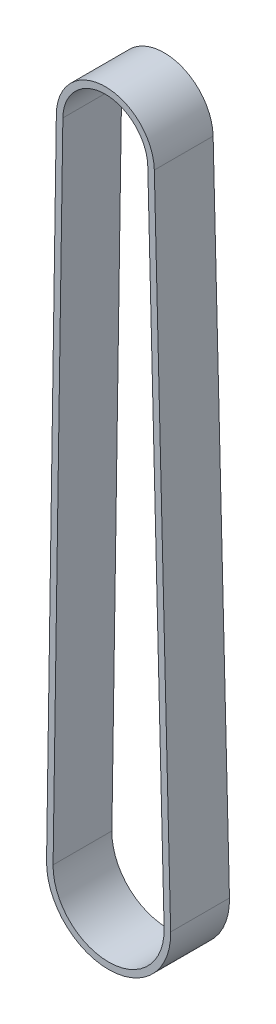
SolidWorks part; units mm, degrees
ref_plane "Front Plane" through (0, 0, 0) normal (0, 0, 1) x (1, 0, 0)
ref_plane "Top Plane" through (0, 0, 0) normal (0, 1, 0) x (1, 0, 0)
ref_plane "Right Plane" through (0, 0, 0) normal (1, 0, 0) x (0, 0, -1)
sketch "Sketch2" plane through (0, 0, 0) normal (0, 0, 1) x (1, 0, 0)
  line L0 (0, 0) -> (1, 0) construction
  line L1 (0, 0) -> (0, 1) construction
  line L2 (6.498, 0.1628) -> (8.9973, -99.5771)
  line L3 (-7.999, -99.6622) -> (-6.4993, 0.0977)
  arc A0 (-6.4993, 0.0977) -> (6.498, 0.1628) centre (0, 0) cw
  arc A1 (8.9973, -99.5771) -> (-7.999, -99.6622) centre (0.5, -99.79) cw
extrude "Extrude-Thin1" add sketch "Sketch2" against normal blind 9 from offset 2 thin
